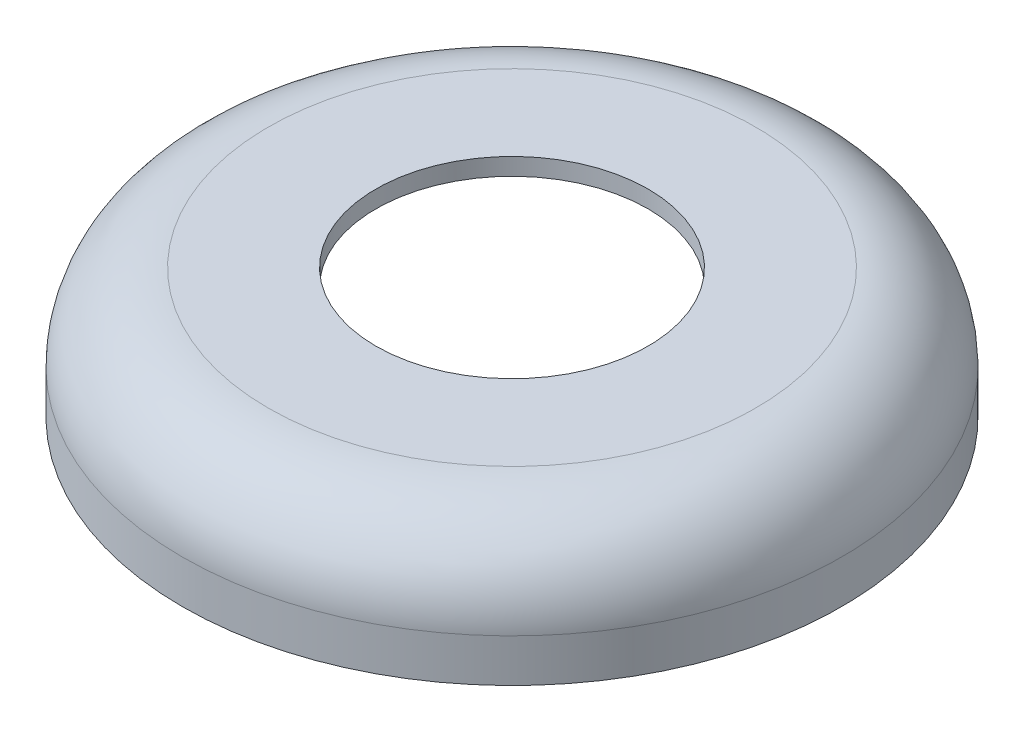
SolidWorks part; units mm, degrees
ref_plane "Front Plane" through (0, 0, 0) normal (0, 0, 1) x (1, 0, 0)
ref_plane "Top Plane" through (0, 0, 0) normal (0, 1, 0) x (1, 0, 0)
ref_plane "Right Plane" through (0, 0, 0) normal (1, 0, 0) x (0, 0, -1)
sketch "Sketch1" plane through (0, 0, 0) normal (0, 1, 0) x (1, 0, 0)
  circle A0 centre (0, 0) radius 11.5
  dimension "D1" = 23
extrude "Boss-Extrude1" add sketch "Sketch1" along normal blind 4.5
fillet "Fillet2" radius 3 1 edges at (0, 4.5, 11.5)
shell "Shell1" thickness 0.6
sketch "Sketch2" plane through (0, 4.5, 0) normal (0, 1, 0) x (1, 0, 0)
  circle A0 centre (0, 0) radius 4.75
  dimension "D1" = 9.5
extrude "Cut-Extrude1" cut sketch "Sketch2" against normal through all
